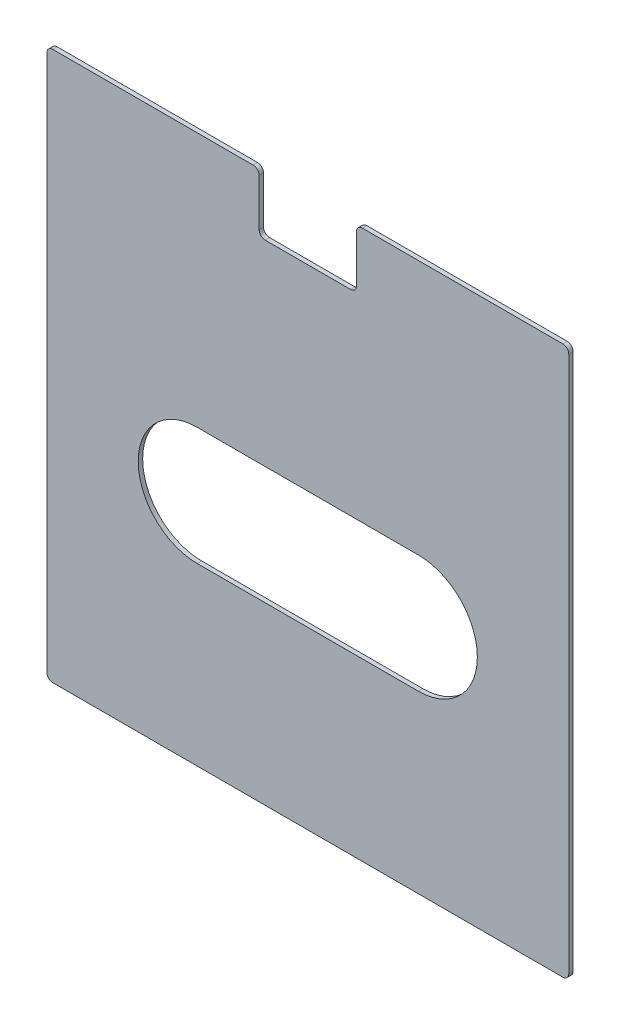
SolidWorks part; units mm, degrees
ref_plane "Front" through (0, 0, 0) normal (0, 0, 1) x (1, 0, 0)
ref_plane "Top" through (0, 0, 0) normal (0, 1, 0) x (1, 0, 0)
ref_plane "Right" through (0, 0, 0) normal (1, 0, 0) x (0, 0, -1)
sketch "Sketch1" plane through (0, 0, 0) normal (0, 0, 1) x (1, 0, 0)
  line L0 (0, 0) -> (177, 0)
  line L1 (177, 0) -> (177, 186)
  line L2 (177, 186) -> (105, 186)
  line L3 (105, 186) -> (105, 166)
  line L4 (105, 166) -> (72, 166)
  line L5 (72, 166) -> (72, 186)
  line L6 (72, 186) -> (0, 186)
  line L7 (0, 186) -> (0, 0)
  line L8 (88.5, 166) -> (88.5, 0) construction
  line L11 (177.5, 1.5) -> (177.5, 184.5) construction
  line L12 (175.5, 186.5) -> (106.5, 186.5) construction
  line L13 (72.5, 184.5) -> (72.5, 168) construction
  line L14 (72.5, 166.5) -> (76.5, 166.5) construction
  dimension "D1" = 0.5
  dimension "D2" = 0.5
  dimension "D3" = 0.5
  dimension "D4" = 0.5
extrude "Boss-Extrude1" add sketch "Sketch1" along normal blind 1.5
fillet "Fillet1" radius 2 8 edges at (105, 166, 0.75) (72, 166, 0.75) (105, 186, 0.75) (72, 186, 0.75) (177, 0, 0.75) (0, 0, 0.75) (177, 186, 0.75) (0, 186, 0.75)
sketch "Sketch2" plane through (0, 0, 0) normal (0, 0, -1) x (-1, 0, 0)
  line L0 (-126, 79.5) -> (-51, 79.5) construction
  line L1 (-126, 99.5) -> (-51, 99.5)
  line L2 (-126, 59.5) -> (-51, 59.5)
  line L4 (-126, 99.5) -> (-51, 99.5) construction
  arc A0 (-126, 99.5) -> (-126, 59.5) centre (-126, 79.5) ccw
  arc A1 (-51, 59.5) -> (-51, 99.5) centre (-51, 79.5) ccw
  point P4 (-88.5, 79.5)
extrude "Cut-Extrude1" cut sketch "Sketch2" against normal blind 10
